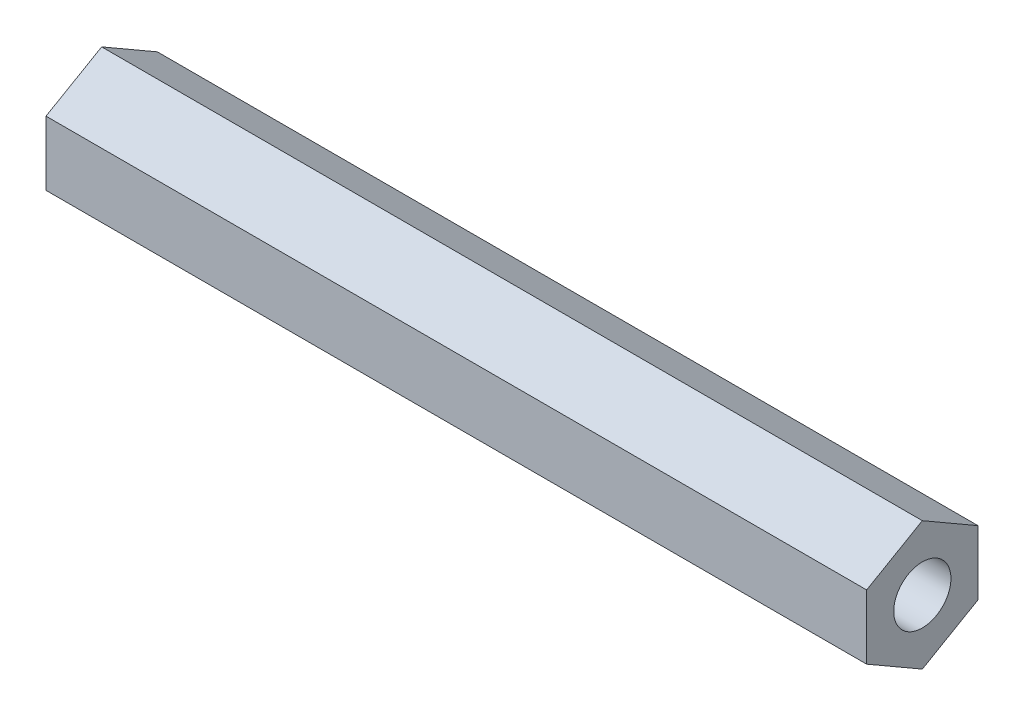
SolidWorks part; units mm, degrees
material "3003 Alloy"
ref_plane "Front Plane" through (0, 0, 0) normal (0, 0, 1) x (1, 0, 0)
ref_plane "Top Plane" through (0, 0, 0) normal (0, 1, 0) x (1, 0, 0)
ref_plane "Right Plane" through (0, 0, 0) normal (1, 0, 0) x (0, 0, -1)
sketch "Sketch1" plane through (0, 0, 0) normal (1, 0, 0) x (0, 0, -1)
  line L1 (0, 7.3323) -> (-6.35, 3.6662)
  line L2 (-6.35, 3.6662) -> (-6.35, -3.6662)
  line L3 (-6.35, -3.6662) -> (0, -7.3323)
  line L4 (0, -7.3323) -> (6.35, -3.6662)
  line L5 (6.35, -3.6662) -> (6.35, 3.6662)
  line L6 (6.35, 3.6662) -> (0, 7.3323)
  circle A0 centre (0, 0) radius 6.35 construction
  circle A1 centre (0, 0) radius 3.2639
  dimension "D1" = 12.7
  dimension "D2" = 6.5278
extrude "Boss-Extrude1" add sketch "Sketch1" along normal blind 93.599
